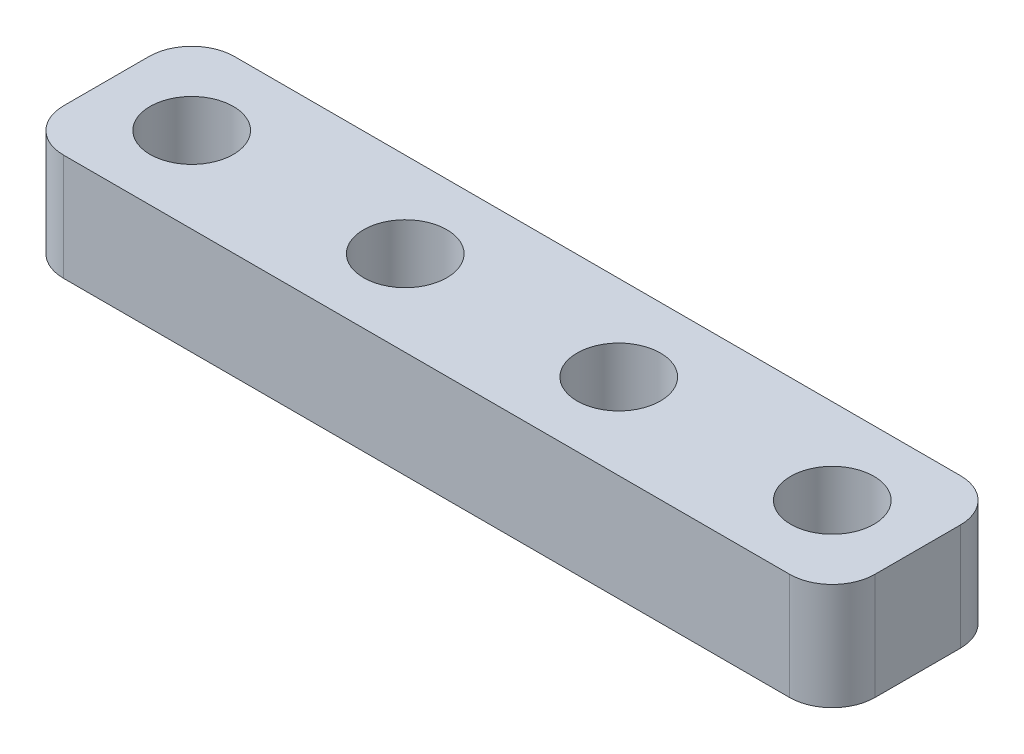
SolidWorks part; units mm, degrees
ref_plane "Front Plane" through (0, 0, 0) normal (0, 0, 1) x (1, 0, 0)
ref_plane "Top Plane" through (0, 0, 0) normal (0, 1, 0) x (1, 0, 0)
ref_plane "Right Plane" through (0, 0, 0) normal (1, 0, 0) x (0, 0, -1)
sketch "Sketch1" plane through (0, 0, 0) normal (0, 1, 0) x (1, 0, 0)
  line L1 (2, 0) -> (36, 0)
  line L2 (0, -2) -> (0, -6)
  line L3 (2, -8) -> (36, -8)
  line L4 (38, -2) -> (38, -6)
  arc A0 (36, -8) -> (38, -6) centre (36, -6) ccw
  arc A1 (0, -6) -> (2, -8) centre (2, -6) ccw
  arc A2 (2, 0) -> (0, -2) centre (2, -2) ccw
  arc A3 (36, 0) -> (38, -2) centre (36, -2) cw
  point P7 (38, -8)
  point P12 (0, 0)
  point P15 (38, 0)
  dimension "D3" = 2
  dimension "D1" = 38
  dimension "D2" = 8
extrude "Boss-Extrude1" add sketch "Sketch1" along normal blind 5
sketch "Sketch2" plane through (0, 5, 0) normal (0, 1, 0) x (1, 0, 0)
  line L2 (34, -4) -> (-16, -4) construction
  line L4 (38, -6) -> (38, -2) construction
  line L7 (36, 0) -> (2, 0) construction
  circle A16 centre (34, -4) radius 1.95
  circle A17 centre (24, -4) radius 1.95
  circle A18 centre (14, -4) radius 1.95
  circle A19 centre (-16, -4) radius 1.95
  circle A20 centre (4, -4) radius 1.95
  circle A21 centre (-6, -4) radius 1.95
  dimension "D1" = 10
  dimension "D4" = 3.9
  dimension "D7" = 3.9
  dimension "D8" = 3.9
  dimension "D9" = 10
  dimension "D10" = 10
  dimension "D11" = 10
  dimension "D12" = 4
  dimension "D13" = 4
  dimension "D6" = 3.9
  dimension "D5" = 3.9
  dimension "D3" = 3.9
  dimension "D2" = 10
extrude "Cut-Extrude1" cut sketch "Sketch2" against normal through all
